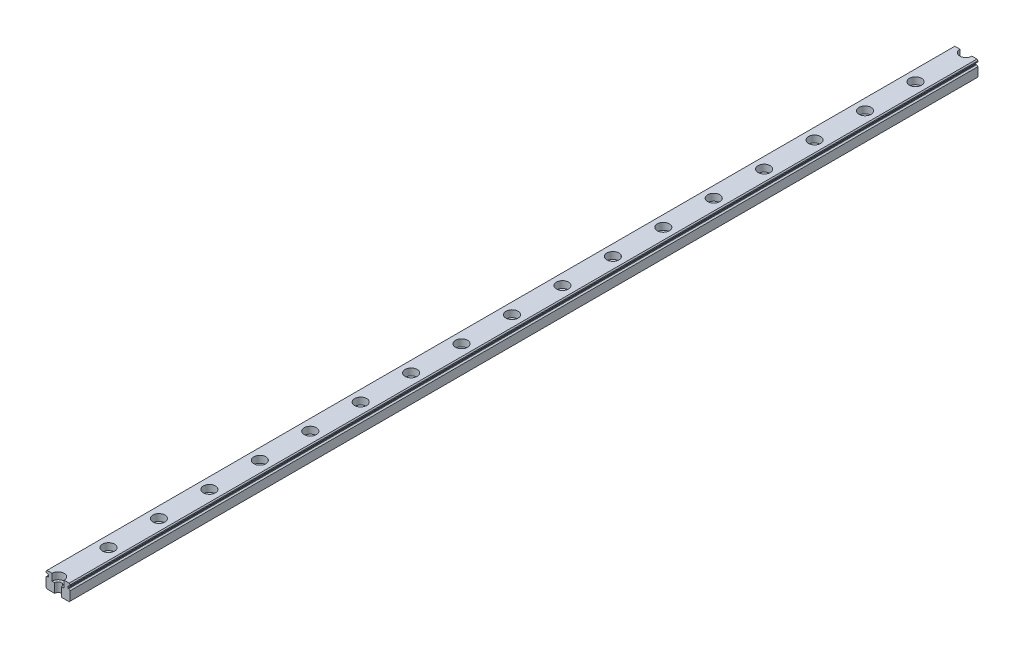
SolidWorks part; units mm, degrees
material "普通碳钢"
ref_plane "前视基准面" through (0, 0, 0) normal (0, 0, 1) x (1, 0, 0)
ref_plane "上视基准面" through (0, 0, 0) normal (0, 1, 0) x (1, 0, 0)
ref_plane "右视基准面" through (0, 0, 0) normal (1, 0, 0) x (0, 0, -1)
sketch "草图1" plane through (0, 0, 0) normal (0, 0, 1) x (1, 0, 0)
  line L1 (-6, -4) -> (6, -4)
  line L2 (-6, -4) -> (-6, 4)
  line L3 (-6, 4) -> (6, 4)
  line L4 (6, -4) -> (6, 4)
  line L5 (-6, -4) -> (6, 4) construction
  line L6 (-6, 4) -> (6, -4) construction
  point P0 (0, 0)
  dimension "D1" = 12
  dimension "D2" = 8
extrude "凸台-拉伸1" add sketch "草图1" along normal mid plane 450
sketch "草图2" plane through (0, 0, -225) normal (0, 0, -1) x (-1, 0, 0)
  line L0 (-7.5, 2) -> (6, 2) construction
  line L2 (6, 4) -> (6, -4) construction
  line L3 (5.2, 2.6) -> (4.8, 2.6)
  line L4 (4.8, 2.6) -> (4.8, 1.4)
  line L5 (4.8, 1.4) -> (5.2, 1.4)
  line L6 (5.2, 1.4) -> (6, 1)
  line L7 (6, 1) -> (6, 3)
  line L8 (6, 3) -> (5.2, 2.6)
  line L9 (-6, 4) -> (6, 4) construction
  dimension "D1" = 1.2
  dimension "D2" = 0.8
  dimension "D3" = 1.2
  dimension "D4" = 0.6
  dimension "D5" = 2
  dimension "D6" = 2
extrude "切除-拉伸1" cut sketch "草图2" against normal through all
mirror "镜向1" about plane through (0, 0, 0) normal (1, 0, 0) of "切除-拉伸1"
chamfer "倒角1" distance 0.5 angle 45 4 edges at (-6, -4, 0) (6, -4, 0) (-6, 4, 0) (6, 4, 0)
hole_wizard "打孔尺寸(%根据)内六角圆柱头螺钉的类型3" positions "草图5" profile "草图6" counterbore size "M3" standard "GB" end condition through all
sketch "草图5" plane through (0, 4, 0) normal (0, 1, 0) x (1, 0, 0)
  point P4 (0, 125)
  point P6 (0, 100)
  point P8 (0, 75)
  point P10 (0, 50)
  point P12 (0, 25)
  point P14 (0, 0)
  point P16 (0, -25)
  point P18 (0, -50)
  point P20 (0, -75)
  point P30 (0, -100)
  point P32 (0, -125)
  point P47 (0, 150)
  point P49 (0, 175)
  point P53 (0, 200)
  point P61 (0, -150)
  point P63 (0, -175)
  point P65 (0, -200)
  point P67 (0, -225)
  point P69 (0, 225)
  point P72 (0, 0)
  point P73 (0, 0)
  dimension "D2" = 25
  dimension "D3" = 25
  dimension "D4" = 25
  dimension "D5" = 25
  dimension "D6" = 25
  dimension "D7" = 25
  dimension "D8" = 25
  dimension "D9" = 25
  dimension "D10" = 25
  dimension "D11" = 25
  dimension "D12" = 25
  dimension "D13" = 25
  dimension "D14" = 25
  dimension "D15" = 25
  dimension "D16" = 25
  dimension "D17" = 25
  dimension "D18" = 25
  dimension "D19" = 25
sketch "草图6" plane through (0, 4, -125) normal (1, 0, 0) x (0, 0, 1)
  line L0 (0, 0) -> (0, 8)
  line L1 (0, 8) -> (1.7, 8)
  line L3 (1.7, 8) -> (1.7, 3.4)
  line L4 (1.7, 3.4) -> (3, 3.4)
  line L5 (3, 3.4) -> (3, 0)
  line L7 (3, 0) -> (0, 0)
  line L11 (0, -6.35) -> (0, 107.95) construction
  dimension "通孔孔直径" = 3.4
  dimension "通孔孔深度" = 8
  dimension "柱形沉头孔直径" = 6
  dimension "柱形沉头孔深度" = 3.4
